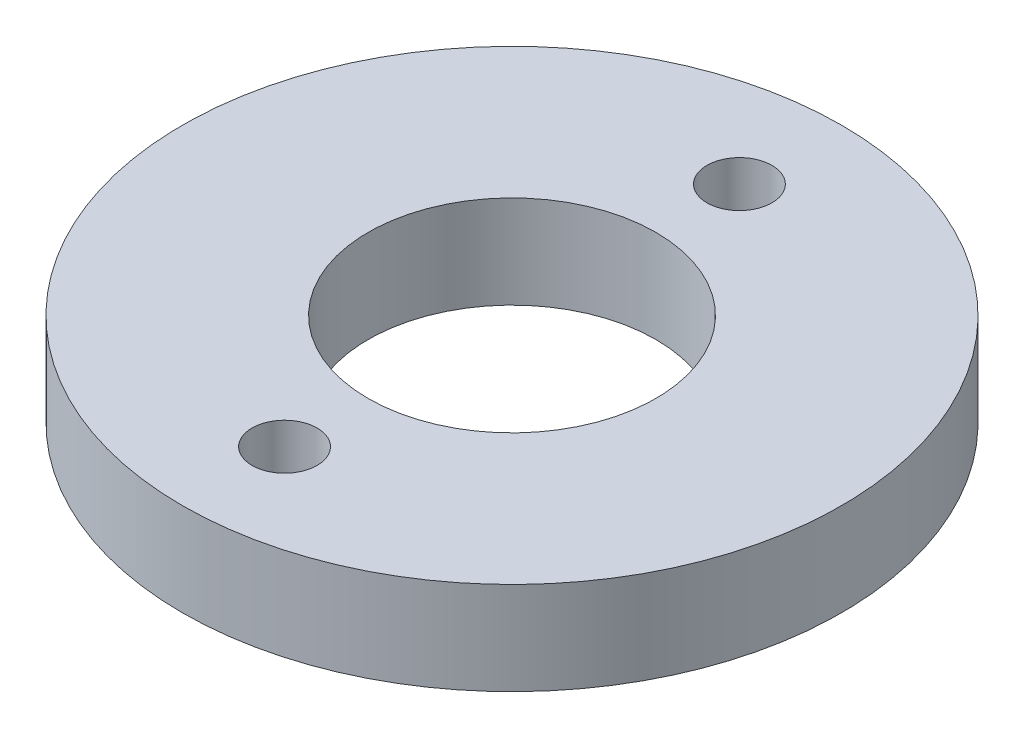
SolidWorks part; units mm, degrees
ref_plane "Front Plane" through (0, 0, 0) normal (0, 0, 1) x (1, 0, 0)
ref_plane "Top Plane" through (0, 0, 0) normal (0, 1, 0) x (1, 0, 0)
ref_plane "Right Plane" through (0, 0, 0) normal (1, 0, 0) x (0, 0, -1)
sketch "Sketch1" plane through (0, 0, 0) normal (0, 1, 0) x (1, 0, 0)
  circle A0 centre (0, 0) radius 10.65
  circle A1 centre (0, 0) radius 4.65
extrude "Boss-Extrude1" add sketch "Sketch1" along normal blind 3
sketch "Sketch2" plane through (0, 3, 0) normal (0, 1, 0) x (1, 0, 0)
  circle A1 centre (0, 7.35) radius 1.05
  circle A2 centre (0, -7.35) radius 1.05
extrude "Cut-Extrude1" cut sketch "Sketch2" against normal blind 3
